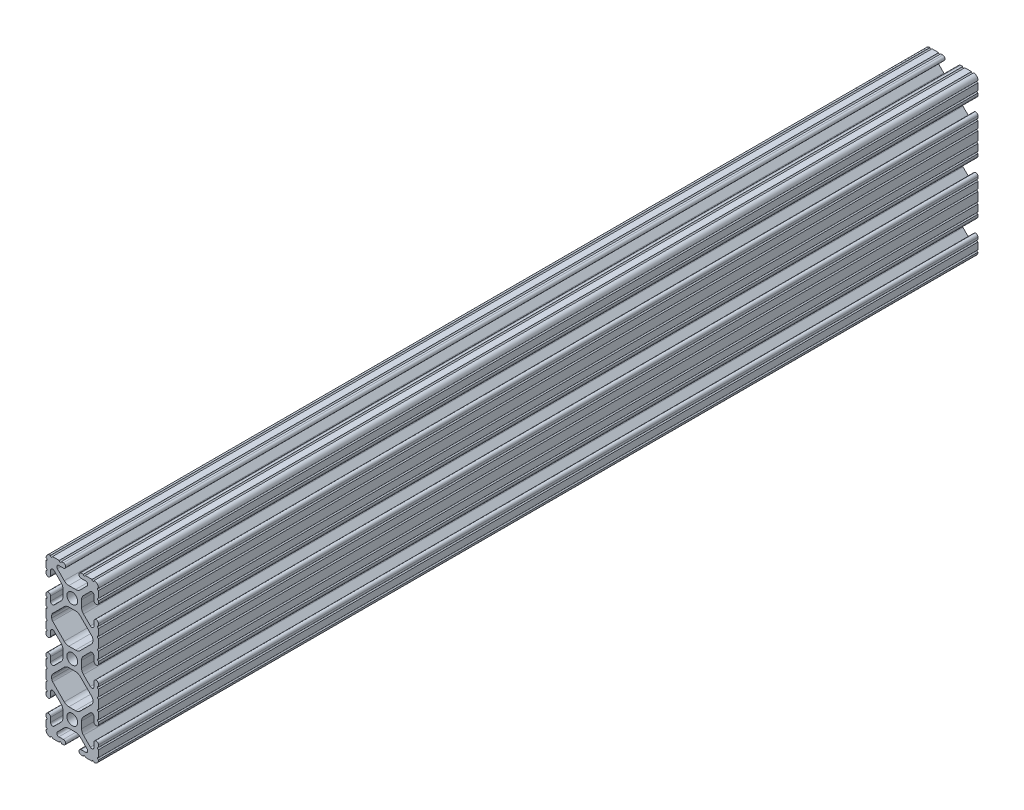
SolidWorks part; units mm, degrees
ref_plane "Front" through (0, 0, 0) normal (0, 0, 1) x (1, 0, 0)
ref_plane "Top" through (0, 0, 0) normal (0, 1, 0) x (1, 0, 0)
ref_plane "Right" through (0, 0, 0) normal (1, 0, 0) x (0, 0, -1)
sketch "Sketch1" plane through (0, 0, 0) normal (0, 0, 1) x (1, 0, 0)
  line L0 (-7.4908, -34.8742) -> (7.4908, -34.8742) construction
  line L1 (-3.1974, -36.9951) -> (3.1974, -36.9951) construction
  line L2 (-7.4908, 34.8742) -> (7.4908, 34.8742) construction
  line L3 (-3.1974, 36.9951) -> (3.1974, 36.9951) construction
  line L16 (-9.9314, -12.1463) -> (-9.9314, -13.2537)
  line L17 (-3.8759, -5.4384) -> (-9.4702, -11.0327)
  line L18 (1.6308, -4.5085) -> (-1.6308, -4.5085)
  line L19 (9.4702, -11.0327) -> (3.8759, -5.4384)
  line L20 (9.9314, -13.2537) -> (9.9314, -12.1463)
  line L21 (3.8759, -19.9616) -> (9.4702, -14.3673)
  line L22 (-1.6308, -20.8915) -> (1.6308, -20.8915)
  line L23 (-9.4702, -14.3673) -> (-3.8759, -19.9616)
  line L32 (-9.9314, 13.2537) -> (-9.9314, 12.1463)
  line L33 (-3.8759, 19.9616) -> (-9.4702, 14.3673)
  line L34 (1.6308, 20.8915) -> (-1.6308, 20.8915)
  line L35 (9.4702, 14.3673) -> (3.8759, 19.9616)
  line L36 (9.9314, 12.1463) -> (9.9314, 13.2537)
  line L37 (3.8759, 5.4384) -> (9.4702, 11.0327)
  line L38 (-1.6308, 4.5085) -> (1.6308, 4.5085)
  line L39 (-9.4702, 11.0327) -> (-3.8759, 5.4384)
  line L152 (-12.7, 34.9504) -> (-12.7, 31.7246)
  line L153 (-12.7, 30.7086) -> (-12.7, 29.7023)
  line L154 (-10.4902, 29.7023) -> (-10.4902, 31.8748)
  line L155 (-8.7558, 32.5932) -> (-5.4384, 29.2759)
  line L156 (-4.5085, 27.0308) -> (-4.5085, 23.7692)
  line L157 (-5.4384, 21.5241) -> (-8.7558, 18.2068)
  line L158 (-10.4902, 18.9252) -> (-10.4902, 21.0977)
  line L159 (-12.7, 21.0977) -> (-12.7, 20.0914)
  line L160 (-12.7, 19.0754) -> (-12.7, 15.8496)
  line L161 (-12.7, 14.8336) -> (-12.7, 10.5664)
  line L162 (-12.7, 9.5504) -> (-12.7, 6.3246)
  line L163 (-12.7, 5.3086) -> (-12.7, 4.3023)
  line L164 (-10.4902, 4.3023) -> (-10.4902, 6.4748)
  line L165 (-8.7558, 7.1932) -> (-5.4384, 3.8759)
  line L166 (-4.5085, 1.6308) -> (-4.5085, -1.6308)
  line L167 (-5.4384, -3.8759) -> (-8.7558, -7.1932)
  line L168 (-10.4902, -6.4748) -> (-10.4902, -4.3023)
  line L169 (-12.7, -4.3023) -> (-12.7, -5.3086)
  line L170 (-12.7, -6.3246) -> (-12.7, -9.5504)
  line L171 (-12.7, -10.5664) -> (-12.7, -14.8336)
  line L172 (-12.7, -15.8496) -> (-12.7, -19.0754)
  line L173 (-12.7, -20.0914) -> (-12.7, -21.0977)
  line L174 (-10.4902, -21.0977) -> (-10.4902, -18.9252)
  line L175 (-8.7558, -18.2068) -> (-5.4384, -21.5241)
  line L176 (-4.5085, -23.7692) -> (-4.5085, -27.0308)
  line L177 (-5.4384, -29.2759) -> (-8.7558, -32.5932)
  line L178 (-10.4902, -31.8748) -> (-10.4902, -29.7023)
  line L179 (-12.7, -29.7023) -> (-12.7, -30.7086)
  line L180 (-12.7, -31.7246) -> (-12.7, -34.9504)
  line L181 (-9.5504, -38.1) -> (-6.3246, -38.1)
  line L182 (-5.3086, -38.1) -> (-4.3023, -38.1)
  line L183 (-4.3023, -35.8902) -> (-6.4748, -35.8902)
  line L184 (-7.1932, -34.1558) -> (-3.8759, -30.8384)
  line L185 (-1.6308, -29.9085) -> (1.6308, -29.9085)
  line L186 (3.8759, -30.8384) -> (7.1932, -34.1558)
  line L187 (6.4748, -35.8902) -> (4.3023, -35.8902)
  line L188 (4.3023, -38.1) -> (5.3086, -38.1)
  line L189 (6.3246, -38.1) -> (9.5504, -38.1)
  line L190 (12.7, -34.9504) -> (12.7, -31.7246)
  line L191 (12.7, -30.7086) -> (12.7, -29.7023)
  line L192 (10.4902, -29.7023) -> (10.4902, -31.8748)
  line L193 (8.7558, -32.5932) -> (5.4384, -29.2759)
  line L194 (4.5085, -27.0308) -> (4.5085, -23.7692)
  line L195 (5.4384, -21.5241) -> (8.7558, -18.2068)
  line L196 (10.4902, -18.9252) -> (10.4902, -21.0977)
  line L197 (12.7, -21.0977) -> (12.7, -20.0914)
  line L198 (12.7, -19.0754) -> (12.7, -15.8496)
  line L199 (12.7, -14.8336) -> (12.7, -10.5664)
  line L200 (12.7, -9.5504) -> (12.7, -6.3246)
  line L201 (12.7, -5.3086) -> (12.7, -4.3023)
  line L202 (10.4902, -4.3023) -> (10.4902, -6.4748)
  line L203 (8.7558, -7.1932) -> (5.4384, -3.8759)
  line L204 (4.5085, -1.6308) -> (4.5085, 1.6308)
  line L205 (5.4384, 3.8759) -> (8.7558, 7.1932)
  line L206 (10.4902, 6.4748) -> (10.4902, 4.3023)
  line L207 (12.7, 4.3023) -> (12.7, 5.3086)
  line L208 (12.7, 6.3246) -> (12.7, 9.5504)
  line L209 (12.7, 10.5664) -> (12.7, 14.8336)
  line L210 (12.7, 15.8496) -> (12.7, 19.0754)
  line L211 (12.7, 20.0914) -> (12.7, 21.0977)
  line L212 (10.4902, 21.0977) -> (10.4902, 18.9252)
  line L213 (8.7558, 18.2068) -> (5.4384, 21.5241)
  line L214 (4.5085, 23.7692) -> (4.5085, 27.0308)
  line L215 (5.4384, 29.2759) -> (8.7558, 32.5932)
  line L216 (10.4902, 31.8748) -> (10.4902, 29.7023)
  line L217 (12.7, 29.7023) -> (12.7, 30.7086)
  line L218 (12.7, 31.7246) -> (12.7, 34.9504)
  line L219 (9.5504, 38.1) -> (6.3246, 38.1)
  line L220 (5.3086, 38.1) -> (4.3023, 38.1)
  line L221 (4.3023, 35.8902) -> (6.4748, 35.8902)
  line L222 (7.1932, 34.1558) -> (3.8759, 30.8384)
  line L223 (1.6308, 29.9085) -> (-1.6308, 29.9085)
  line L224 (-3.8759, 30.8384) -> (-7.1932, 34.1558)
  line L225 (-6.4748, 35.8902) -> (-4.3023, 35.8902)
  line L226 (-4.3023, 38.1) -> (-5.3086, 38.1)
  line L227 (-6.3246, 38.1) -> (-9.5504, 38.1)
  circle A2 centre (0, -25.4) radius 2.6035
  circle A4 centre (0, 0) radius 2.6035
  circle A6 centre (0, 25.4) radius 2.6035
  arc A18 (-9.9314, -13.2537) -> (-9.4702, -14.3673) centre (-8.3566, -13.2537) ccw
  arc A19 (-9.4702, -11.0327) -> (-9.9314, -12.1463) centre (-8.3566, -12.1463) ccw
  arc A20 (-1.6308, -4.5085) -> (-3.8759, -5.4384) centre (-1.6308, -7.6835) ccw
  arc A21 (3.8759, -5.4384) -> (1.6308, -4.5085) centre (1.6308, -7.6835) ccw
  arc A22 (9.9314, -12.1463) -> (9.4702, -11.0327) centre (8.3566, -12.1463) ccw
  arc A23 (9.4702, -14.3673) -> (9.9314, -13.2537) centre (8.3566, -13.2537) ccw
  arc A24 (1.6308, -20.8915) -> (3.8759, -19.9616) centre (1.6308, -17.7165) ccw
  arc A25 (-3.8759, -19.9616) -> (-1.6308, -20.8915) centre (-1.6308, -17.7165) ccw
  arc A36 (-9.9314, 12.1463) -> (-9.4702, 11.0327) centre (-8.3566, 12.1463) ccw
  arc A37 (-9.4702, 14.3673) -> (-9.9314, 13.2537) centre (-8.3566, 13.2537) ccw
  arc A38 (-1.6308, 20.8915) -> (-3.8759, 19.9616) centre (-1.6308, 17.7165) ccw
  arc A39 (3.8759, 19.9616) -> (1.6308, 20.8915) centre (1.6308, 17.7165) ccw
  arc A40 (9.9314, 13.2537) -> (9.4702, 14.3673) centre (8.3566, 13.2537) ccw
  arc A41 (9.4702, 11.0327) -> (9.9314, 12.1463) centre (8.3566, 12.1463) ccw
  arc A42 (1.6308, 4.5085) -> (3.8759, 5.4384) centre (1.6308, 7.6835) ccw
  arc A43 (-3.8759, 5.4384) -> (-1.6308, 4.5085) centre (-1.6308, 7.6835) ccw
  arc A168 (-10.5664, 38.1) -> (-12.7, 35.9664) centre (-10.592, 35.992) ccw
  arc A169 (-12.7, 34.9504) -> (-12.7, 35.9664) centre (-12.7, 35.4584) ccw
  arc A170 (-12.7, 30.7086) -> (-12.7, 31.7246) centre (-12.7, 31.2166) ccw
  arc A171 (-12.7, 29.7023) -> (-10.4902, 29.7023) centre (-11.5951, 29.7023) ccw
  arc A172 (-8.7558, 32.5932) -> (-10.4902, 31.8748) centre (-9.4742, 31.8748) ccw
  arc A173 (-4.5085, 27.0308) -> (-5.4384, 29.2759) centre (-7.6835, 27.0308) ccw
  arc A174 (-5.4384, 21.5241) -> (-4.5085, 23.7692) centre (-7.6835, 23.7692) ccw
  arc A175 (-10.4902, 18.9252) -> (-8.7558, 18.2068) centre (-9.4742, 18.9252) ccw
  arc A176 (-10.4902, 21.0977) -> (-12.7, 21.0977) centre (-11.5951, 21.0977) ccw
  arc A177 (-12.7, 19.0754) -> (-12.7, 20.0914) centre (-12.7, 19.5834) ccw
  arc A178 (-12.7, 14.8336) -> (-12.7, 15.8496) centre (-12.7, 15.3416) ccw
  arc A179 (-12.7, 9.5504) -> (-12.7, 10.5664) centre (-12.7, 10.0584) ccw
  arc A180 (-12.7, 5.3086) -> (-12.7, 6.3246) centre (-12.7, 5.8166) ccw
  arc A181 (-12.7, 4.3023) -> (-10.4902, 4.3023) centre (-11.5951, 4.3023) ccw
  arc A182 (-8.7558, 7.1932) -> (-10.4902, 6.4748) centre (-9.4742, 6.4748) ccw
  arc A183 (-4.5085, 1.6308) -> (-5.4384, 3.8759) centre (-7.6835, 1.6308) ccw
  arc A184 (-5.4384, -3.8759) -> (-4.5085, -1.6308) centre (-7.6835, -1.6308) ccw
  arc A185 (-10.4902, -6.4748) -> (-8.7558, -7.1932) centre (-9.4742, -6.4748) ccw
  arc A186 (-10.4902, -4.3023) -> (-12.7, -4.3023) centre (-11.5951, -4.3023) ccw
  arc A187 (-12.7, -6.3246) -> (-12.7, -5.3086) centre (-12.7, -5.8166) ccw
  arc A188 (-12.7, -10.5664) -> (-12.7, -9.5504) centre (-12.7, -10.0584) ccw
  arc A189 (-12.7, -15.8496) -> (-12.7, -14.8336) centre (-12.7, -15.3416) ccw
  arc A190 (-12.7, -20.0914) -> (-12.7, -19.0754) centre (-12.7, -19.5834) ccw
  arc A191 (-12.7, -21.0977) -> (-10.4902, -21.0977) centre (-11.5951, -21.0977) ccw
  arc A192 (-8.7558, -18.2068) -> (-10.4902, -18.9252) centre (-9.4742, -18.9252) ccw
  arc A193 (-4.5085, -23.7692) -> (-5.4384, -21.5241) centre (-7.6835, -23.7692) ccw
  arc A194 (-5.4384, -29.2759) -> (-4.5085, -27.0308) centre (-7.6835, -27.0308) ccw
  arc A195 (-10.4902, -31.8748) -> (-8.7558, -32.5932) centre (-9.4742, -31.8748) ccw
  arc A196 (-10.4902, -29.7023) -> (-12.7, -29.7023) centre (-11.5951, -29.7023) ccw
  arc A197 (-12.7, -31.7246) -> (-12.7, -30.7086) centre (-12.7, -31.2166) ccw
  arc A198 (-12.7, -35.9664) -> (-12.7, -34.9504) centre (-12.7, -35.4584) ccw
  arc A199 (-12.7, -35.9664) -> (-10.5664, -38.1) centre (-10.592, -35.992) ccw
  arc A200 (-9.5504, -38.1) -> (-10.5664, -38.1) centre (-10.0584, -38.1) ccw
  arc A201 (-5.3086, -38.1) -> (-6.3246, -38.1) centre (-5.8166, -38.1) ccw
  arc A202 (-4.3023, -38.1) -> (-4.3023, -35.8902) centre (-4.3023, -36.9951) ccw
  arc A203 (-7.1932, -34.1558) -> (-6.4748, -35.8902) centre (-6.4748, -34.8742) ccw
  arc A204 (-1.6308, -29.9085) -> (-3.8759, -30.8384) centre (-1.6308, -33.0835) ccw
  arc A205 (3.8759, -30.8384) -> (1.6308, -29.9085) centre (1.6308, -33.0835) ccw
  arc A206 (6.4748, -35.8902) -> (7.1932, -34.1558) centre (6.4748, -34.8742) ccw
  arc A207 (4.3023, -35.8902) -> (4.3023, -38.1) centre (4.3023, -36.9951) ccw
  arc A208 (6.3246, -38.1) -> (5.3086, -38.1) centre (5.8166, -38.1) ccw
  arc A209 (10.5664, -38.1) -> (9.5504, -38.1) centre (10.0584, -38.1) ccw
  arc A210 (10.5664, -38.1) -> (12.7, -35.9664) centre (10.592, -35.992) ccw
  arc A211 (12.7, -34.9504) -> (12.7, -35.9664) centre (12.7, -35.4584) ccw
  arc A212 (12.7, -30.7086) -> (12.7, -31.7246) centre (12.7, -31.2166) ccw
  arc A213 (12.7, -29.7023) -> (10.4902, -29.7023) centre (11.5951, -29.7023) ccw
  arc A214 (8.7558, -32.5932) -> (10.4902, -31.8748) centre (9.4742, -31.8748) ccw
  arc A215 (4.5085, -27.0308) -> (5.4384, -29.2759) centre (7.6835, -27.0308) ccw
  arc A216 (5.4384, -21.5241) -> (4.5085, -23.7692) centre (7.6835, -23.7692) ccw
  arc A217 (10.4902, -18.9252) -> (8.7558, -18.2068) centre (9.4742, -18.9252) ccw
  arc A218 (10.4902, -21.0977) -> (12.7, -21.0977) centre (11.5951, -21.0977) ccw
  arc A219 (12.7, -19.0754) -> (12.7, -20.0914) centre (12.7, -19.5834) ccw
  arc A220 (12.7, -14.8336) -> (12.7, -15.8496) centre (12.7, -15.3416) ccw
  arc A221 (12.7, -9.5504) -> (12.7, -10.5664) centre (12.7, -10.0584) ccw
  arc A222 (12.7, -5.3086) -> (12.7, -6.3246) centre (12.7, -5.8166) ccw
  arc A223 (12.7, -4.3023) -> (10.4902, -4.3023) centre (11.5951, -4.3023) ccw
  arc A224 (8.7558, -7.1932) -> (10.4902, -6.4748) centre (9.4742, -6.4748) ccw
  arc A225 (4.5085, -1.6308) -> (5.4384, -3.8759) centre (7.6835, -1.6308) ccw
  arc A226 (5.4384, 3.8759) -> (4.5085, 1.6308) centre (7.6835, 1.6308) ccw
  arc A227 (10.4902, 6.4748) -> (8.7558, 7.1932) centre (9.4742, 6.4748) ccw
  arc A228 (10.4902, 4.3023) -> (12.7, 4.3023) centre (11.5951, 4.3023) ccw
  arc A229 (12.7, 6.3246) -> (12.7, 5.3086) centre (12.7, 5.8166) ccw
  arc A230 (12.7, 10.5664) -> (12.7, 9.5504) centre (12.7, 10.0584) ccw
  arc A231 (12.7, 15.8496) -> (12.7, 14.8336) centre (12.7, 15.3416) ccw
  arc A232 (12.7, 20.0914) -> (12.7, 19.0754) centre (12.7, 19.5834) ccw
  arc A233 (12.7, 21.0977) -> (10.4902, 21.0977) centre (11.5951, 21.0977) ccw
  arc A234 (8.7558, 18.2068) -> (10.4902, 18.9252) centre (9.4742, 18.9252) ccw
  arc A235 (4.5085, 23.7692) -> (5.4384, 21.5241) centre (7.6835, 23.7692) ccw
  arc A236 (5.4384, 29.2759) -> (4.5085, 27.0308) centre (7.6835, 27.0308) ccw
  arc A237 (10.4902, 31.8748) -> (8.7558, 32.5932) centre (9.4742, 31.8748) ccw
  arc A238 (10.4902, 29.7023) -> (12.7, 29.7023) centre (11.5951, 29.7023) ccw
  arc A239 (12.7, 31.7246) -> (12.7, 30.7086) centre (12.7, 31.2166) ccw
  arc A240 (12.7, 35.9664) -> (12.7, 34.9504) centre (12.7, 35.4584) ccw
  arc A241 (12.7, 35.9664) -> (10.5664, 38.1) centre (10.592, 35.992) ccw
  arc A242 (9.5504, 38.1) -> (10.5664, 38.1) centre (10.0584, 38.1) ccw
  arc A243 (5.3086, 38.1) -> (6.3246, 38.1) centre (5.8166, 38.1) ccw
  arc A244 (4.3023, 38.1) -> (4.3023, 35.8902) centre (4.3023, 36.9951) ccw
  arc A245 (7.1932, 34.1558) -> (6.4748, 35.8902) centre (6.4748, 34.8742) ccw
  arc A246 (1.6308, 29.9085) -> (3.8759, 30.8384) centre (1.6308, 33.0835) ccw
  arc A247 (-3.8759, 30.8384) -> (-1.6308, 29.9085) centre (-1.6308, 33.0835) ccw
  arc A248 (-6.4748, 35.8902) -> (-7.1932, 34.1558) centre (-6.4748, 34.8742) ccw
  arc A249 (-4.3023, 35.8902) -> (-4.3023, 38.1) centre (-4.3023, 36.9951) ccw
  arc A250 (-6.3246, 38.1) -> (-5.3086, 38.1) centre (-5.8166, 38.1) ccw
  arc A251 (-10.5664, 38.1) -> (-9.5504, 38.1) centre (-10.0584, 38.1) ccw
extrude "Boss-Extrude1" add sketch "Sketch1" along normal mid plane 425.45
